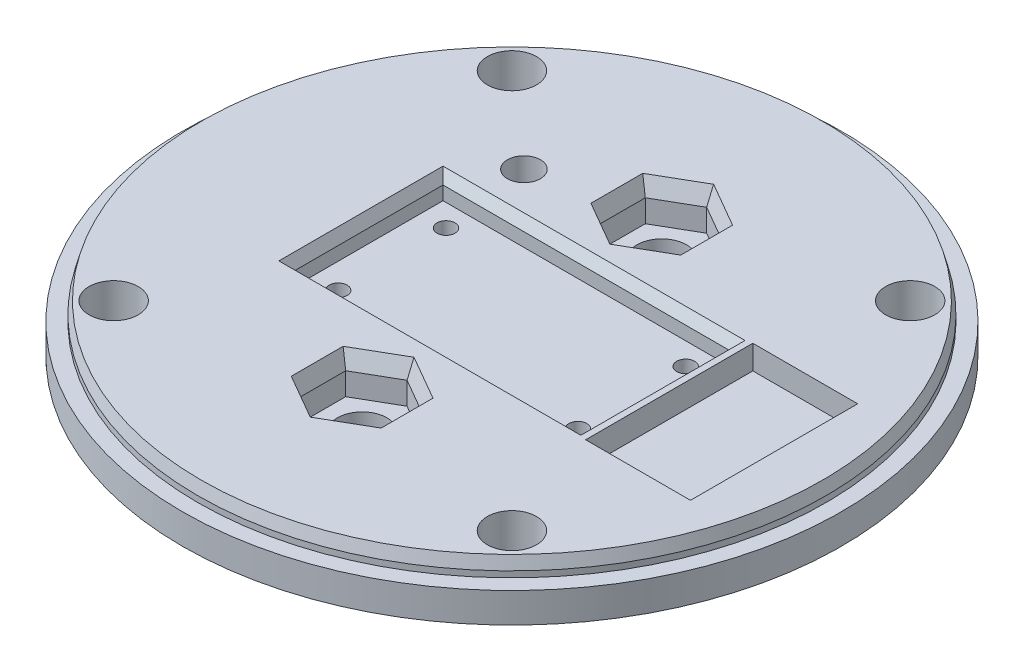
SolidWorks part; units mm, degrees
ref_plane "Спереди" through (0, 0, 0) normal (0, 0, 1) x (1, 0, 0)
ref_plane "Сверху" through (0, 0, 0) normal (0, 1, 0) x (1, 0, 0)
ref_plane "Справа" through (0, 0, 0) normal (1, 0, 0) x (0, 0, -1)
sketch "Эскиз1" plane through (0, 0, 0) normal (0, 1, 0) x (1, 0, 0)
  circle A0 centre (0, 0) radius 55
  dimension "D1" = 110
extrude "Бобышка-Вытянуть1" add sketch "Эскиз1" along normal blind 5
sketch "Эскиз2" plane through (0, 5, 0) normal (0, 1, 0) x (1, 0, 0)
  circle A0 centre (0, 0) radius 52.4
  dimension "D1" = 104.8
extrude "Бобышка-Вытянуть2" add sketch "Эскиз2" along normal blind 3
sketch "Эскиз3" plane through (0, 0, 0) normal (0, -1, 0) x (1, 0, 0)
  line L1 (17.5, -15) -> (-17.5, -15)
  line L2 (17.5, -15) -> (17.5, 15)
  line L3 (17.5, 15) -> (-17.5, 15)
  line L4 (-17.5, -15) -> (-17.5, 15)
  line L5 (17.5, -15) -> (-17.5, 15) construction
  line L6 (17.5, 15) -> (-17.5, -15) construction
  point P0 (0, 0)
  dimension "D1" = 35
  dimension "D2" = 30
extrude "Бобышка-Вытянуть3" add sketch "Эскиз3" along normal blind 25
sketch "Эскиз5" plane through (0, 0, 0) normal (0, -1, 0) x (1, 0, 0)
  line L1 (33.234, -33.234) -> (-33.234, -33.234) construction
  line L2 (33.234, -33.234) -> (33.234, 33.234) construction
  line L3 (33.234, 33.234) -> (-33.234, 33.234) construction
  line L4 (-33.234, -33.234) -> (-33.234, 33.234) construction
  line L5 (33.234, -33.234) -> (-33.234, 33.234) construction
  line L6 (33.234, 33.234) -> (-33.234, -33.234) construction
  circle A1 centre (33.234, -33.234) radius 4.1
  circle A2 centre (-33.234, -33.234) radius 4.1
  circle A3 centre (-33.234, 33.234) radius 4.1
  circle A4 centre (33.234, 33.234) radius 4.1
  circle A5 centre (0, 0) radius 47 construction
  circle A6 centre (0, 0) radius 55 construction
  point P0 (0, 0)
  dimension "D1" = 8
  dimension "D2" = 8.2
extrude "Вырез-Вытянуть2" cut sketch "Эскиз5" against normal through all
sketch "Эскиз6" plane through (0, 8, 0) normal (0, 1, 0) x (1, 0, 0)
  line L0 (0, 0) -> (0, 52.4) construction
  line L1 (0, 20) -> (-18, 20) construction
  circle A0 centre (0, 0) radius 52.4 construction
  circle A1 centre (-18, 20) radius 2.75
  dimension "D3" = 5.5
  dimension "D1" = 20
  dimension "D2" = 18
extrude "Вырез-Вытянуть3" cut sketch "Эскиз6" against normal through all
sketch "Sketch2" plane through (-17.5, 0, 0) normal (-1, 0, 0) x (0, 0, 1)
  line L0 (-15, -25) -> (15, 0) construction
  line L2 (10.125, -17.675) -> (-10.125, -17.675)
  line L3 (10.125, -17.675) -> (10.125, -7.325)
  line L4 (10.125, -7.325) -> (-10.125, -7.325)
  line L5 (-10.125, -17.675) -> (-10.125, -7.325)
  line L6 (10.125, -17.675) -> (-10.125, -7.325) construction
  line L7 (10.125, -7.325) -> (-10.125, -17.675) construction
  point P2 (0, -12.5)
  point P10 (0, -12.5)
  dimension "D1" = 20.25
  dimension "D2" = 10.35
extrude "Cut-Extrude1" cut sketch "Sketch2" against normal through all
sketch "Sketch3" plane through (0, 8, 0) normal (0, 1, 0) x (1, 0, 0)
  line L0 (52.4, 0) -> (-52.4, 0) construction
  line L2 (26.25, 13.95) -> (43.75, 13.95)
  line L3 (26.25, 13.95) -> (26.25, -13.95)
  line L4 (26.25, -13.95) -> (43.75, -13.95)
  line L5 (43.75, 13.95) -> (43.75, -13.95)
  line L6 (26.25, 13.95) -> (43.75, -13.95) construction
  line L7 (26.25, -13.95) -> (43.75, 13.95) construction
  line L8 (-24.2, 12.7) -> (24.2, 12.7)
  line L9 (-24.2, 12.7) -> (-24.2, -12.7)
  line L10 (-24.2, -12.7) -> (24.2, -12.7)
  line L11 (24.2, 12.7) -> (24.2, -12.7)
  line L12 (-24.2, 12.7) -> (24.2, -12.7) construction
  line L13 (-24.2, -12.7) -> (24.2, 12.7) construction
  circle A0 centre (0, 0) radius 52.4 construction
  circle A1 centre (0, 0) radius 52.4 construction
  point P8 (0, 0)
  point P13 (0, 0)
  point P22 (35, 0)
  dimension "D1" = 17.5
  dimension "D2" = 27.9
  dimension "D3" = 35
  dimension "D4" = 48.4
  dimension "D5" = 25.4
extrude "Cut-Extrude2" cut sketch "Sketch3" against normal blind 4
chamfer "Chamfer1" distance 2 angle 15 1 edges at (0, 8, 52.4)
sketch "Sketch4" plane through (0, -25, 0) normal (0, -1, 0) x (1, 0, 0)
  line L0 (-17.5, 0) -> (17.5, 0) construction
  line L1 (-17.5, 15) -> (-17.5, -15) construction
  line L2 (17.5, -15) -> (17.5, 15) construction
  line L4 (17.5, -15) -> (-17.5, -15)
  line L5 (17.5, -15) -> (17.5, 15)
  line L6 (17.5, 15) -> (-17.5, 15)
  line L7 (-17.5, -15) -> (-17.5, 15)
  line L8 (17.5, -15) -> (-17.5, 15) construction
  line L9 (17.5, 15) -> (-17.5, -15) construction
  point P6 (0, 0)
extrude "Cut-Extrude3" cut sketch "Sketch4" against normal blind 12.5
sketch "Sketch5" plane through (0, -7.325, 0) normal (0, -1, 0) x (1, 0, 0)
  line L0 (0, 10.125) -> (0, -10.125) construction
  line L1 (17.5, 10.125) -> (-17.5, 10.125) construction
  line L2 (17.5, -10.125) -> (-17.5, -10.125) construction
  line L4 (10, -35) -> (-10, -35)
  line L5 (10, -35) -> (10, 35)
  line L6 (10, 35) -> (-10, 35)
  line L7 (-10, -35) -> (-10, 35)
  line L8 (10, -35) -> (-10, 35) construction
  line L9 (10, 35) -> (-10, -35) construction
  point P6 (0, 0)
  dimension "D1" = 20
  dimension "D2" = 70
extrude "Boss-Extrude2" add sketch "Sketch5" against normal up to surface (5.325 mm away) from offset 2 up to face at (-18, 0, -17.25) offset against normal yes
sketch "Sketch6" plane through (0, -5.325, 0) normal (0, -1, 0) x (1, 0, 0)
  line L0 (10, 25) -> (-10, 25) construction
  line L1 (10, 15) -> (10, 35) construction
  line L2 (-10, 35) -> (-10, 15) construction
  line L3 (10, -25) -> (-10, -25) construction
  line L4 (10, -35) -> (10, -15) construction
  line L5 (-10, -15) -> (-10, -35) construction
  circle A0 centre (0, 25) radius 4.15
  circle A1 centre (0, -25) radius 4.15
  dimension "D3" = 8.3
  dimension "D1" = 10
  dimension "D2" = 10
  dimension "D4" = 25
extrude "Cut-Extrude4" cut sketch "Sketch6" against normal through all
sketch "Sketch7" plane through (0, 8, 0) normal (0, 1, 0) x (1, 0, 0)
  line L1 (0, -32.5) -> (6.4952, -28.75)
  line L2 (6.4952, -28.75) -> (6.4952, -21.25)
  line L3 (6.4952, -21.25) -> (0, -17.5)
  line L4 (0, -17.5) -> (-6.4952, -21.25)
  line L5 (-6.4952, -21.25) -> (-6.4952, -28.75)
  line L6 (-6.4952, -28.75) -> (0, -32.5)
  line L7 (0, 17.5) -> (6.4952, 21.25)
  line L8 (6.4952, 21.25) -> (6.4952, 28.75)
  line L9 (6.4952, 28.75) -> (0, 32.5)
  line L10 (0, 32.5) -> (-6.4952, 28.75)
  line L11 (-6.4952, 28.75) -> (-6.4952, 21.25)
  line L12 (-6.4952, 21.25) -> (0, 17.5)
  circle A0 centre (0, -25) radius 7.5 construction
  circle A1 centre (0, 25) radius 7.5 construction
  dimension "D1" = 15
extrude "Cut-Extrude5" cut sketch "Sketch7" against normal blind 6.5
chamfer "Chamfer2" distance 1 angle 70 12 edges at (3.2476, 8, 19.375) (6.4952, 8, 25) (3.2476, 8, 30.625) (-3.2476, 8, 30.625) (-6.4952, 8, 25) (-3.2476, 8, 19.375) (3.2476, 8, -19.375) (6.4952, 8, -25) (3.2476, 8, -30.625) (-3.2476, 8, -30.625) (-6.4952, 8, -25) (-3.2476, 8, -19.375)
sketch "Sketch8" plane through (0, 4, 0) normal (0, 1, 0) x (1, 0, 0)
  line L0 (20, -12.7) -> (20, 12.7) construction
  line L1 (-24.2, -12.7) -> (24.2, -12.7) construction
  line L2 (24.2, 12.7) -> (-24.2, 12.7) construction
  line L3 (-20, 12.7) -> (-20, -12.7) construction
  line L4 (20, -12.7) -> (-20, 12.7) construction
  line L5 (20, 9) -> (-20, 9) construction
  line L6 (20, -9) -> (-20, -9) construction
  line L7 (0, 9) -> (0, -9) construction
  circle A0 centre (20, 9) radius 1.5
  circle A1 centre (20, -9) radius 1.5
  circle A2 centre (-20, 9) radius 1.5
  circle A3 centre (-20, -9) radius 1.5
  point P8 (0, 0)
  point P20 (0, 0)
  dimension "D2" = 3
  dimension "D1" = 40
  dimension "D3" = 18
extrude "Cut-Extrude6" cut sketch "Sketch8" against normal through all
chamfer "Chamfer3" distance 1 angle 60 4 edges at (24.2, 8, 0) (0, 8, 12.7) (-24.2, 8, 0) (0, 8, -12.7)
